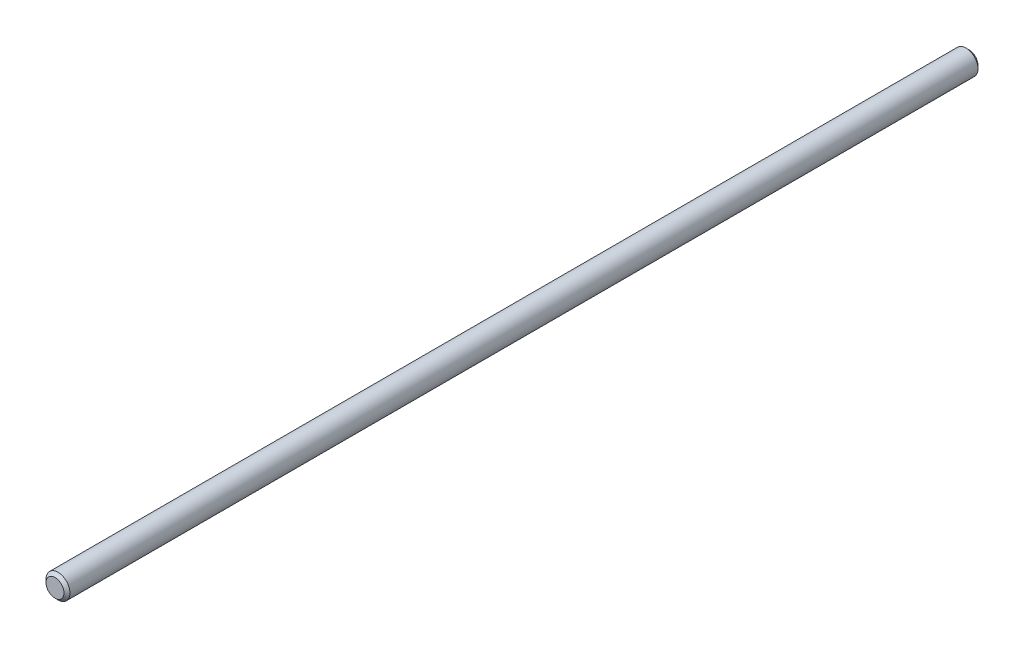
SolidWorks part; units mm, degrees
material "1060 Alloy"
ref_plane "Front" through (0, 0, 0) normal (0, 0, 1) x (1, 0, 0)
ref_plane "Top" through (0, 0, 0) normal (0, 1, 0) x (1, 0, 0)
ref_plane "Right" through (0, 0, 0) normal (1, 0, 0) x (0, 0, -1)
sketch "Sketch1" plane through (0, 0, 0) normal (0, 0, 1) x (1, 0, 0)
  circle A0 centre (0, 0) radius 4
  dimension "D1" = 8
extrude "Boss-Extrude1" add sketch "Sketch1" along normal blind 305
chamfer "Chamfer2" distance 1 angle 45 1 edges at (4, 0, 0)
chamfer "Chamfer3" distance 1 angle 45 1 edges at (4, 0, 305)
